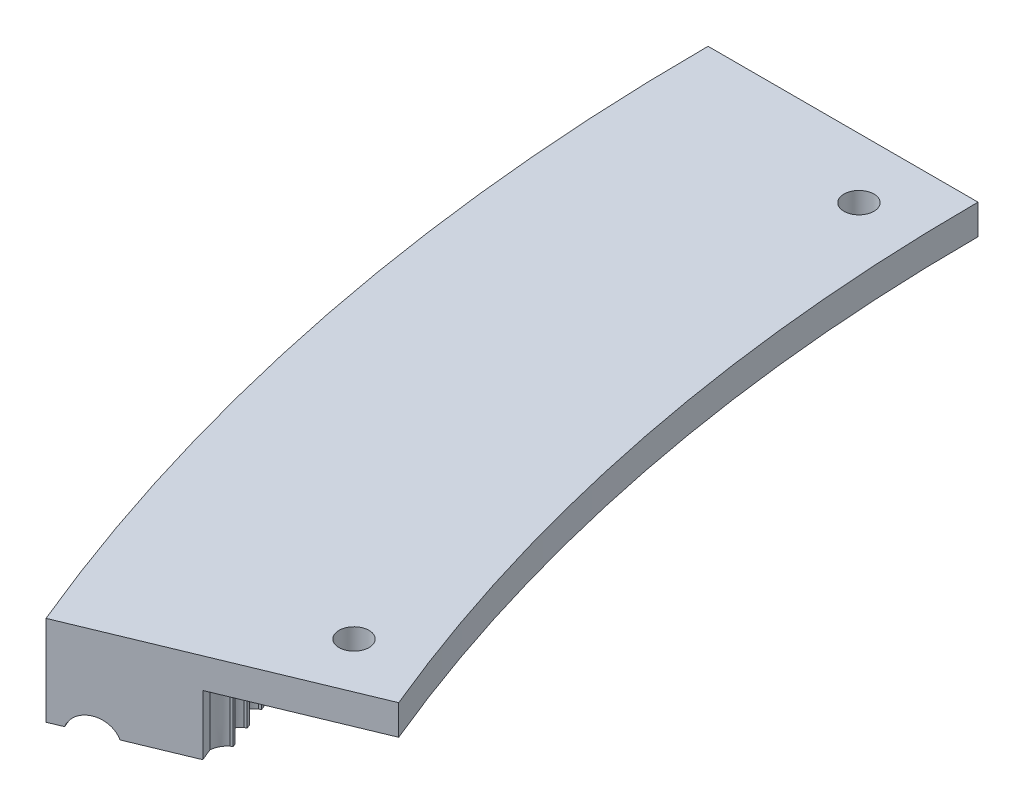
SolidWorks part; units mm, degrees
ref_plane "Front Plane" through (0, 0, 0) normal (0, 0, 1) x (1, 0, 0)
ref_plane "Top Plane" through (0, 0, 0) normal (0, 1, 0) x (1, 0, 0)
ref_plane "Right Plane" through (0, 0, 0) normal (1, 0, 0) x (0, 0, -1)
sketch "Sketch3" plane through (0, 0, 0) normal (0, 0, 1) x (1, 0, 0)
  line L0 (-400.05, 0) -> (-457.2, 0)
  line L1 (-457.2, 0) -> (-457.2, -19.05)
  line L4 (-425.45, -6.35) -> (-400.05, -6.35)
  line L5 (-400.05, -6.35) -> (-400.05, 0)
  line L6 (-425.45, -6.35) -> (-431.8, -6.35)
  line L8 (-431.8, -6.35) -> (-431.8, -19.05)
  line L9 (-457.2, -19.05) -> (-454.1917, -19.05)
  line L10 (-445.2115, -19.05) -> (-431.8, -19.05)
  line L11 (-459.5466, -20.6375) -> (-428.4704, -20.6375) construction
  arc A5 (-445.2115, -19.05) -> (-454.1917, -19.05) centre (-449.7016, -20.6375) ccw
  dimension "D1" = 19.05
  dimension "D3" = 31.75
  dimension "D6" = 1.5875
  dimension "D2" = 57.15
  dimension "D4" = 6.35
  dimension "D5" = 457.2
sketch "Sketch5" plane through (0, 0, 0) normal (0, 0, 1) x (1, 0, 0)
  line L0 (0, 0) -> (0, 189.1302) construction
revolve "Revolve1" add sketch "Sketch3" angle 22.5 about L0
sketch "Sketch7" plane through (0, -6.35, 0) normal (0, -1, 0) x (1, 0, 0)
  line L0 (-431.8, 0) -> (-400.05, 0) construction
  line L1 (-398.9312, 165.2427) -> (-369.598, 153.0925) construction
  circle A0 centre (-412.5546, 12.7) radius 3.175
  arc A1 (-369.598, 153.0925) -> (-400.05, 0) centre (0, 0) ccw construction
  circle A5 centre (-386.0108, 146.1445) radius 3.175
  dimension "D1" = 12.7
  dimension "D3" = 412.75
  dimension "D2" = 412.75
  dimension "D4" = 12.7
extrude "Cut-Extrude1" cut sketch "Sketch7" against normal through all
sketch "Sketch10" plane through (0, -6.35, 0) normal (0, -1, 0) x (1, 0, 0)
  line L0 (-429.4397, -0.4637) -> (-428.9268, -0.4369)
  line L1 (-429.4159, 0.4445) -> (-428.9052, 0.3908)
  arc A0 (-428.9052, 0.3908) -> (-428.9268, -0.4369) centre (-421.9854, -0.2045) ccw
  arc A2 (-431.8436, 2.6029) -> (-431.8454, -2.2788) centre (0, 0) ccw
  spline S0 degree 3 poles (-431.8454, -2.2788) (-431.2358, -1.3311) (-430.4343, -0.7262) (-429.4397, -0.4637) knots 0.132959 0.132959 0.132959 0.132959 1 1 1 1
  spline S1 degree 3 poles (-431.8436, 2.6029) (-431.2764, 1.501) (-430.4668, 0.7816) (-429.4159, 0.4445) knots 0.069618 0.069618 0.069618 0.069618 1 1 1 1
extrude "Boss-Extrude1" add sketch "Sketch10" along normal blind 12.7
pattern_circular "CirPattern1" count 32 over 21.8 of "Boss-Extrude1"
